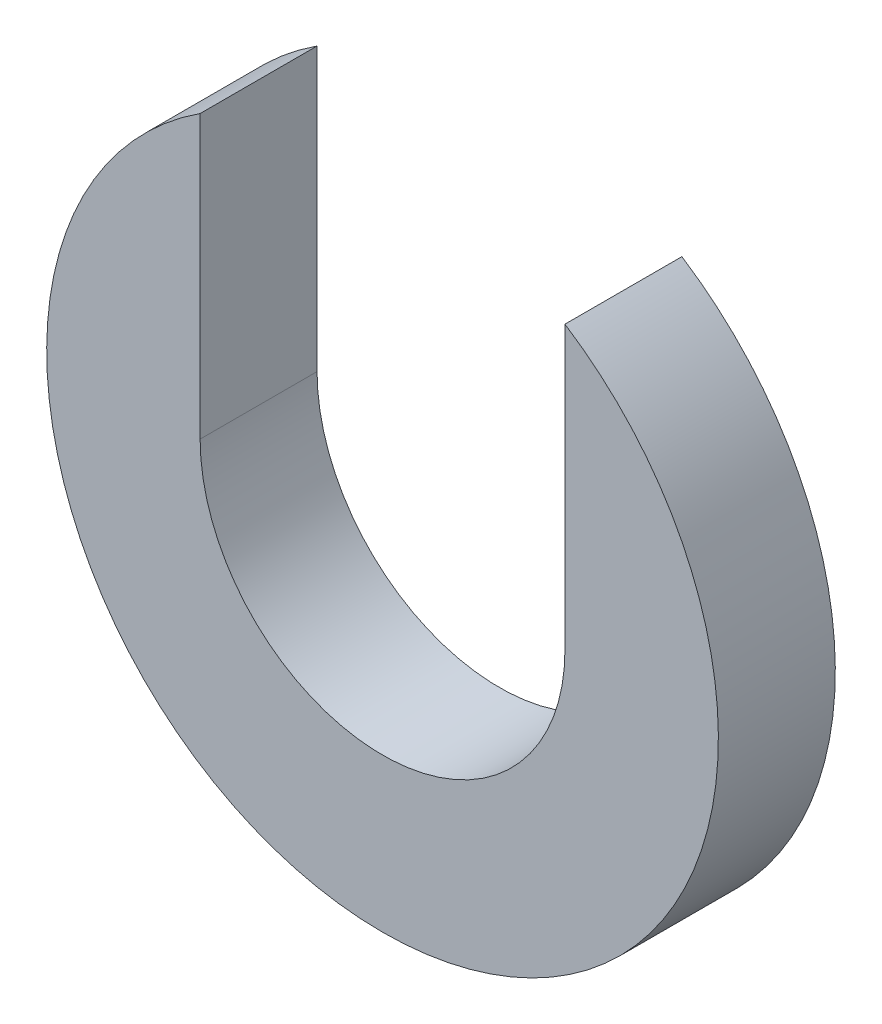
SolidWorks part; units mm, degrees
ref_plane "Front Plane" through (0, 0, 0) normal (0, 0, 1) x (1, 0, 0)
ref_plane "Top Plane" through (0, 0, 0) normal (0, 1, 0) x (1, 0, 0)
ref_plane "Right Plane" through (0, 0, 0) normal (1, 0, 0) x (0, 0, -1)
sketch "Sketch1" plane through (0, 0, 0) normal (0, 0, 1) x (1, 0, 0)
  line L0 (-4.953, 0) -> (-4.953, 7.6562)
  line L1 (4.953, 0) -> (4.953, 7.6562)
  arc A0 (-4.953, 7.6562) -> (4.953, 7.6562) centre (0, 0) ccw
  arc A1 (-4.953, 0) -> (4.953, 0) centre (0, 0) ccw
  dimension "D1" = 9.1186
  dimension "D2" = 9.906
extrude "Boss-Extrude1" add sketch "Sketch1" along normal blind 3.175
